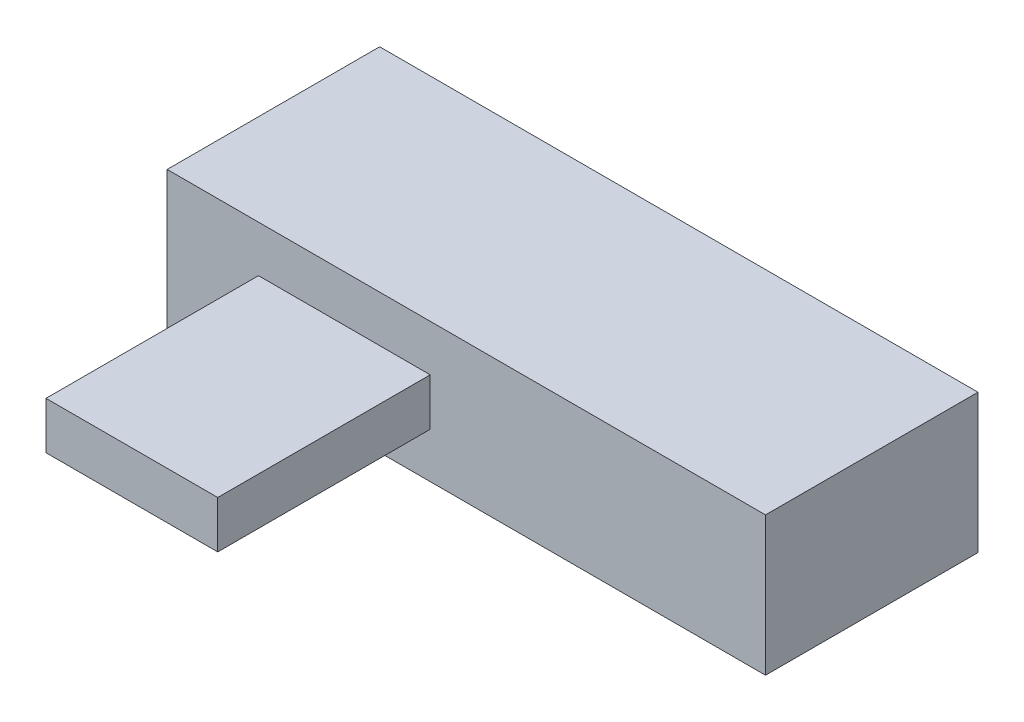
SolidWorks part; units mm, degrees
ref_plane "Front Plane" through (0, 0, 0) normal (0, 0, 1) x (1, 0, 0)
ref_plane "Top Plane" through (0, 0, 0) normal (0, 1, 0) x (1, 0, 0)
ref_plane "Right Plane" through (0, 0, 0) normal (1, 0, 0) x (0, 0, -1)
sketch "Sketch1" plane through (0, 0, 0) normal (0, 0, 1) x (1, 0, 0)
  line L1 (-65.2319, 21.744) -> (112.1835, 21.744)
  line L2 (-65.2319, 21.744) -> (-65.2319, -19.4349)
  line L3 (-65.2319, -19.4349) -> (112.1835, -19.4349)
  line L4 (112.1835, 21.744) -> (112.1835, -19.4349)
extrude "Boss-Extrude1" add sketch "Sketch1" along normal blind 63
sketch "Sketch2" plane through (0, 0, 63) normal (0, 0, 1) x (1, 0, 0)
  line L1 (-38.1622, 8) -> (12.7628, 8)
  line L2 (-38.1622, 8) -> (-38.1622, -5.9844)
  line L3 (-38.1622, -5.9844) -> (12.7628, -5.9844)
  line L4 (12.7628, 8) -> (12.7628, -5.9844)
extrude "Boss-Extrude2" add sketch "Sketch2" along normal blind 63
